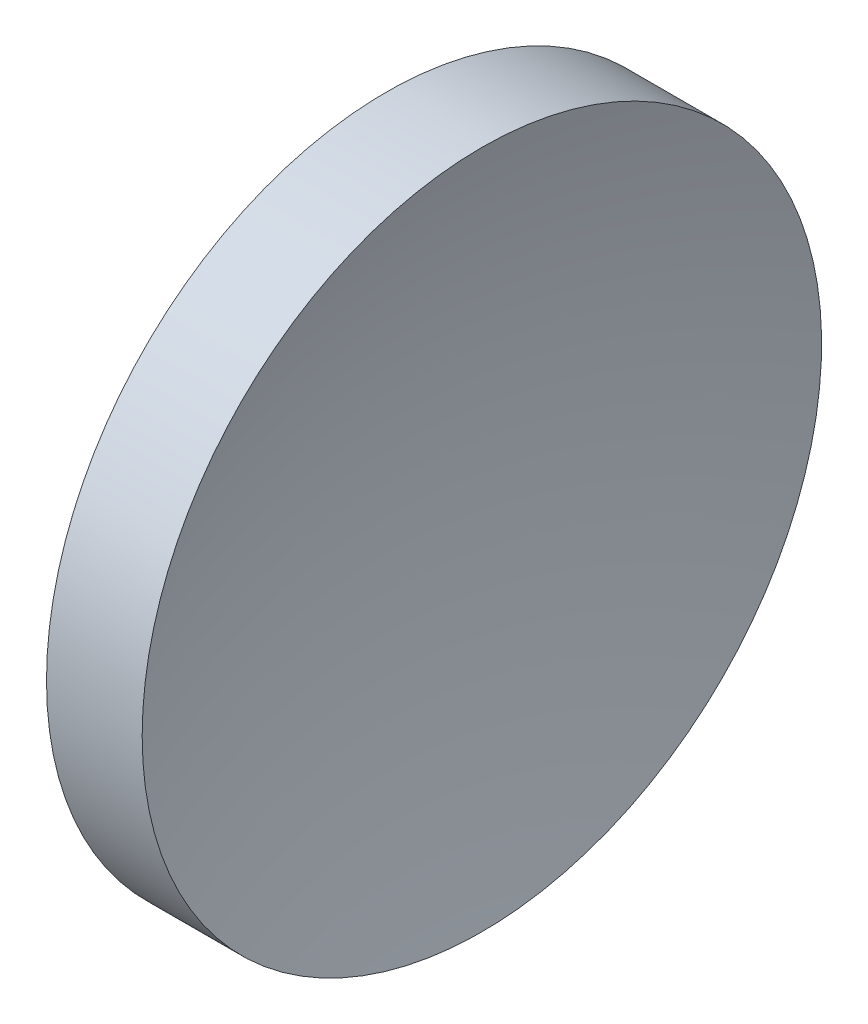
SolidWorks part; units mm, degrees
ref_plane "前视基准面" through (0, 0, 0) normal (0, 0, 1) x (1, 0, 0)
ref_plane "上视基准面" through (0, 0, 0) normal (0, 1, 0) x (1, 0, 0)
ref_plane "右视基准面" through (0, 0, 0) normal (1, 0, 0) x (0, 0, -1)
sketch "草图1" plane through (0, 0, 0) normal (0, 0, 1) x (1, 0, 0)
  line L0 (105.6218, 65.1556) -> (137.1869, 65.1556) construction
  line L1 (113.7199, 65.1556) -> (113.7199, 87.6556)
  line L2 (113.7199, 87.6556) -> (120.057, 87.6556)
  line L3 (116.7199, 65.1556) -> (113.7199, 65.1556)
  arc A0 (120.057, 87.6556) -> (116.7199, 65.1556) centre (194.2399, 65.1556) ccw
revolve "旋转1" add sketch "草图1" angle 360 about L0
